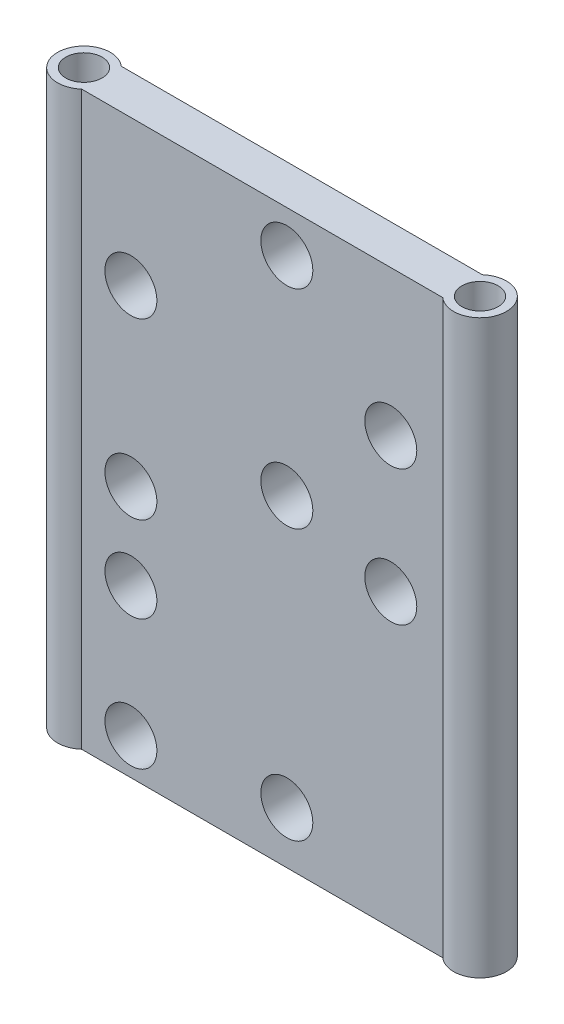
SolidWorks part; units mm, degrees
ref_plane "Front Plane" through (0, 0, 0) normal (0, 0, 1) x (1, 0, 0)
ref_plane "Top Plane" through (0, 0, 0) normal (0, 1, 0) x (1, 0, 0)
ref_plane "Right Plane" through (0, 0, 0) normal (1, 0, 0) x (0, 0, -1)
sketch "Sketch1" plane through (0, 0, 0) normal (0, 1, 0) x (1, 0, 0)
  line L1 (-38.1, -3.81) -> (38.1, -3.81)
  line L2 (-38.1, -3.81) -> (-38.1, 3.81)
  line L3 (-38.1, 3.81) -> (38.1, 3.81)
  line L4 (38.1, -3.81) -> (38.1, 3.81)
  line L5 (-38.1, -3.81) -> (38.1, 3.81) construction
  line L6 (-38.1, 3.81) -> (38.1, -3.81) construction
  circle A0 centre (-38.1, 0) radius 5.08
  circle A1 centre (38.1, 0) radius 5.08
  circle A2 centre (-38.1, 0) radius 3.4925
  circle A3 centre (38.1, 0) radius 3.4925
  point P0 (0, 0)
  dimension "D3" = 10.16
  dimension "D4" = 6.985
  dimension "D1" = 7.62
  dimension "D2" = 76.2
extrude "Boss-Extrude1" add sketch "Sketch1" along normal mid plane 110 contours A2 L2 L3 A0 L1 | A2 L2 L1 A0 L3 | A1 L3 A0 L1 | A3 L4 L1 A1 L3 | A3 L4 L3 A1 L1
sketch "Sketch5" plane through (0, 0, 3.81) normal (0, 0, 1) x (1, 0, 0)
  line L0 (-25.2601, -23) -> (-25.2601, -48) construction
  line L5 (-25.2601, 27) -> (24.7399, 27) construction
  line L7 (-15.2601, -45) -> (24.7399, -45) construction
  line L8 (-15.2601, -45) -> (-15.2601, 47) construction
  line L9 (-15.2601, 47) -> (24.7399, 47) construction
  line L10 (24.7399, -45) -> (24.7399, 47) construction
  line L11 (34.7399, 55) -> (34.7399, -55) construction
  line L12 (-34.7399, -55) -> (34.7399, -55) construction
  line L14 (24.7399, 47) -> (-25.2601, 47) construction
  line L15 (24.7399, 47) -> (24.7399, -23) construction
  line L16 (24.7399, -23) -> (-25.2601, -23) construction
  line L17 (-25.2601, 47) -> (-25.2601, -23) construction
  circle A4 centre (-25.2601, -48) radius 5
  circle A5 centre (-25.2601, -23) radius 5
  circle A12 centre (4.7399, 47) radius 5
  circle A14 centre (4.7399, -45) radius 5
  circle A15 centre (24.7399, 1) radius 5
  circle A19 centre (-25.2601, 27) radius 5
  circle A20 centre (24.7399, 27) radius 5
  circle A21 centre (-25.2601, -6.5) radius 5
  circle A22 centre (4.7399, 7) radius 5
  dimension "D4" = 20
  dimension "D7" = 40
  dimension "D1" = 70
  dimension "D2" = 50
  dimension "D3" = 25
  dimension "D5" = 40
  dimension "D6" = 92
  dimension "D8" = 10
  dimension "D9" = 10
extrude "Cut-Extrude2" cut sketch "Sketch5" against normal through all
